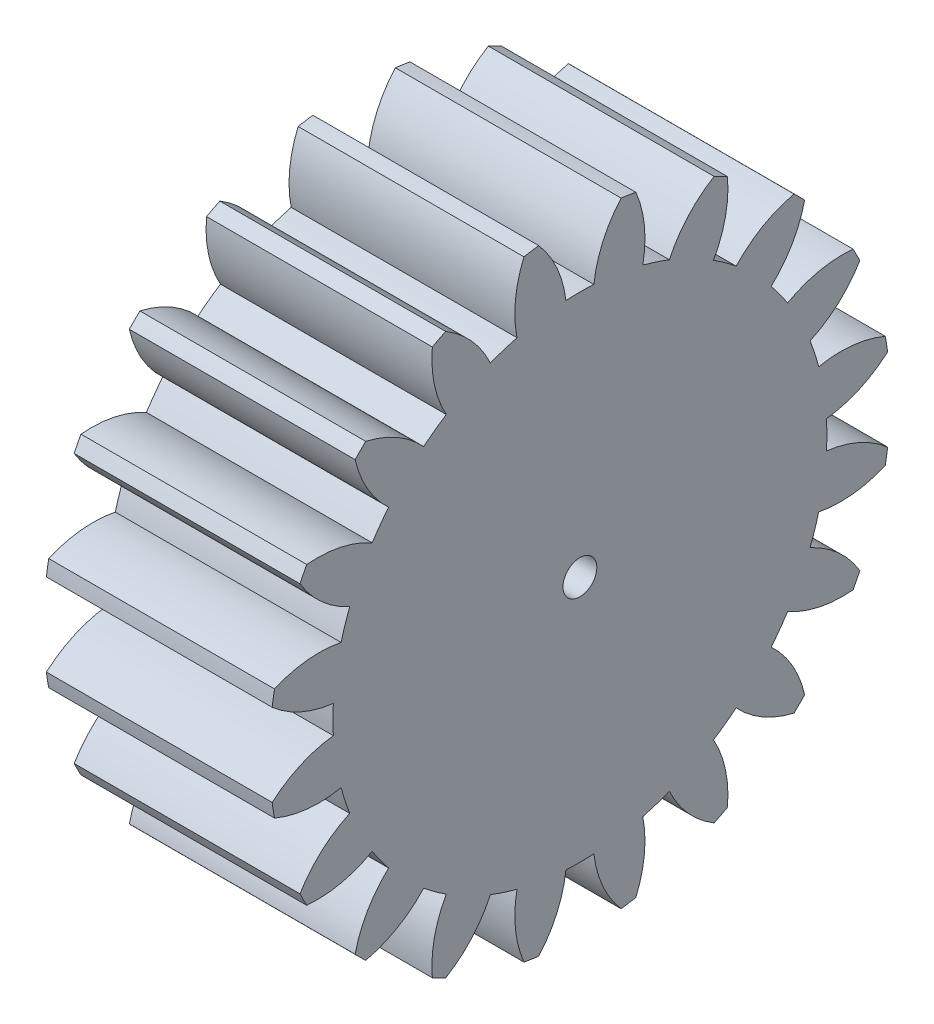
SolidWorks part; units mm, degrees
ref_plane "Plane1" through (0, 0, 0) normal (0, 0, 1) x (1, 0, 0)
ref_plane "Plane2" through (0, 0, 0) normal (0, 1, 0) x (1, 0, 0)
ref_plane "Plane3" through (0, 0, 0) normal (1, 0, 0) x (0, 0, -1)
sketch "HoldingSke" plane through (0, 0, 0) normal (0, 1, 0) x (1, 0, 0)
  line L0 (0, 0) -> (0.3759, -0.1368)
  line L1 (-15, 0) -> (100, 0) construction
  line L2 (0, 0) -> (-2.1039, 2.3779)
  line L3 (0, 0) -> (-11.863, 4.5341)
  line L4 (0, 0) -> (8.1152, 2.9537)
  line L5 (0, 0) -> (-46.8476, -17.4728)
  line L6 (0, 0) -> (-16.5793, -11.1861)
  line L7 (-2.1039, 2.3779) -> (8.6586, 51.2059)
  line L8 (-76.2, 54.61) -> (-75.7, 54.61)
  line L9 (-71.009, 38.7566) -> (-53.1078, 45.2721)
  line L10 (-76.2, 71.12) -> (104.1128, 71.12)
  line L11 (0, 0) -> (-20, 0)
  line L12 (-76.2, 101.6) -> (-76.113, 101.6)
  line L13 (24.9733, 27.94) -> (52.9518, 28.4284)
  line L14 (24.9733, 27.94) -> (24.9743, 27.94)
  line L15 (24.9733, 27.94) -> (100.4006, 29.5858)
  line L16 (-63.627, -2.5) -> (-12.827, -2.5)
  circle A0 centre (0, 0) radius 1.5
  circle A1 centre (0, 0) radius 21.874
  circle A2 centre (0, 0) radius 37.5
  circle A3 centre (0, 0) radius 1.5
  dimension "MHD" = 43.748
  dimension "Hub_dia" = 75
  dimension "Bore" = 3
  dimension "MBD" = 3
  dimension "Num_teeth" = 20
  dimension "Pitch" = 0.4
  dimension "Overall_len" = 50
  dimension "Show_teeth" = 20
  dimension "Thickness" = 20
  dimension "OAL" = 50.0001
  dimension "T_dim" = 0.5
  dimension "Ap" = 20
  dimension "H" = 19.05
  dimension "Pitch_radius" = 180.3128
  dimension "Width" = 20
  dimension "Backlash" = 0.087
  dimension "Addendum_fac" = 1
  dimension "Dedendum_fac" = 1.25
  dimension "Clearance_fac" = 0.25
  dimension "Dedendum_add" = 0.001
  dimension "Module" = 2.5
sketch "BasProSke" plane through (0, 0, 0) normal (0, 1, 0) x (1, 0, 0)
  line L0 (-10, 0) -> (60, 0) construction
  line L1 (0, 0) -> (0, 27.5)
  line L2 (0, 0) -> (20, 0)
  line L3 (20, 0) -> (20, 27.5)
  line L4 (20, 27.5) -> (0, 27.5)
  dimension "Thickness" = 20
  dimension "Diameter" = 55
revolve "Base-Revolve" add sketch "BasProSke" angle 360 about L0
sketch "TooCutSke" plane through (0, 0, 0) normal (1, 0, 0) x (0, 0, -1)
  line L1 (0, 0) -> (0, 107) construction
  line L2 (0, 0) -> (-2.1137, 24.9105) construction
  line L3 (0, 0) -> (-7.8012, 49.2549) construction
  line L4 (-2.1137, 24.9105) -> (-3.9006, 24.6275) construction
  arc A0 (1.2377, 21.839) -> (-1.2377, 21.839) centre (0, 0) ccw
  arc A1 (3.6672, 27.28) -> (-3.6672, 27.28) centre (0, 0) ccw
  circle A2 centre (0, 0) radius 25 construction
  circle A3 centre (0, 0) radius 23.4923 construction
  arc A4 (-1.2377, 21.839) -> (-3.6672, 27.28) centre (-11.1689, 20.6675) ccw
  arc A5 (3.6672, 27.28) -> (1.2377, 21.839) centre (11.1689, 20.6675) ccw
  dimension "Root_dia" = 43.748
  dimension "Overcut_dia" = 55.0508
  dimension "Pitch_dia" = 50
  dimension "Base_dia" = 46.9846
  dimension "Flank_rad" = 10
  dimension "Half_ang" = 9
  dimension "Half_CT" = 1.8092
extrude "ToothCut" cut sketch "TooCutSke" along normal through all
fillet "Breaks" [suppressed] radius 0.05
fillet "RootFillets" [suppressed] radius 0.626
pattern_circular "TeethCuts" count 20 every 18 about axis through (-10, 0, 0) along (1, 0, 0) of "ToothCut", "RootFillets", "Breaks"
sketch "HubNeaOneSke" plane through (0, 0, 0) normal (-1, 0, 0) x (0, 0, 1)
  circle A0 centre (0, 0) radius 21.874
  dimension "Diameter" = 43.748
extrude "HubNearOne" [suppressed] add sketch "HubNeaOneSke" along normal blind 30.0001
sketch "HubNeaBotSke" plane through (0, 0, 0) normal (-1, 0, 0) x (0, 0, 1)
  circle A0 centre (0, 0) radius 21.874
  dimension "Diameter" = 43.748
extrude "HubNearBoth" [suppressed] add sketch "HubNeaBotSke" along normal blind 15
ref_plane "FarPln" through (20, 0, 0) normal (1, 0, 0) x (0, 0, -1)
sketch "HubFarSke" plane through (20, 0, 0) normal (1, 0, 0) x (0, 0, -1)
  circle A0 centre (0, 0) radius 21.874
  dimension "Diameter" = 43.748
extrude "HubFar" [suppressed] add sketch "HubFarSke" along normal blind 15
sketch "BorSke" plane through (0, 0, 0) normal (1, 0, 0) x (0, 0, -1)
  circle A0 centre (0, 0) radius 1.5
  dimension "Diameter" = 3
extrude "Bore" cut sketch "BorSke" along normal mid plane 100.0001
sketch "KeySke" plane through (0, 0, 0) normal (1, 0, 0) x (0, 0, -1)
  line L0 (-0.6, 0) -> (-0.6, 2)
  line L1 (-0.6, 2) -> (0.6, 2)
  line L2 (0.6, 2) -> (0.6, 0)
  line L3 (0, 0) -> (0, 34) construction
  line L4 (-0.6, 0) -> (0.6, 0)
  dimension "Offset" = 2
  dimension "Width" = 1.2
extrude "Keyway" [suppressed] cut sketch "KeySke" along normal mid plane 100.0001
pattern_circular "Keyway2" [suppressed] count 2 every 90 about axis through (-10, 0, 0) along (1, 0, 0)
equation "' \"Module@HoldingSke\" = 6.35"
equation "' \"Num_teeth@HoldingSke\" = 12"
equation "' \"Ap@HoldingSke\" =  20"
equation "' \"Ap@HoldingSke\" = 20"
equation "' \"Width@HoldingSke\" = 0.5 * 25.4"
equation "' \"Hub_dia@HoldingSke\"= 1 * 25.4"
equation "' \"Hub_dia@HoldingSke\" = 1 * 25.4"
equation "' \"Overall_len@HoldingSke\" = 1.0 * 25.4"
equation "' \"Bore@HoldingSke\" = 0.75 * 25.4"
equation "' \"T_dim@HoldingSke\" = 0.1 * 25.4"
equation "' \"Width@KeySke\" = 0.25 * 25.4"
equation "' \"Show_teeth@HoldingSke\" = 13"
equation "' \"Backlash@HoldingSke\" = 0.009 * 25.4"
equation "' \"Addendum_fac@HoldingSke\" = 1.0"
equation "' \"Dedendum_fac@HoldingSke\" = 1.25"
equation "' \"Dedendum_add@HoldingSke\" = 0.00005 * 25.4"
equation "' \"Clearance_fac@HoldingSke\" = 0.25"
equation "\"Pitch@HoldingSke\" = 1 / \"Module@HoldingSke\""
equation "\"Overcut_dia@TooCutSke\" = (\"Num_teeth@HoldingSke\" + 2 * \"Addendum_fac@HoldingSke\") / \"Pitch@HoldingSke\" + 0.002 * 25.4"
equation "\"Pitch_dia@TooCutSke\" = \"Num_teeth@HoldingSke\" / \"Pitch@HoldingSke\""
equation "\"Base_dia@TooCutSke\" = \"Num_teeth@HoldingSke\" / \"Pitch@HoldingSke\" * cos((\"Ap@HoldingSke\"  * 3.14159265 / 180))"
equation "\"Root_dia@TooCutSke\" = (\"Num_teeth@HoldingSke\" + 2) / \"Pitch@HoldingSke\" - 2 * (\"Addendum_fac@HoldingSke\" + \"Dedendum_fac@HoldingSke\") / \"Pitch@HoldingSke\" - \"Dedendum_add@HoldingSke\" * 2"
equation "\"Half_ang@TooCutSke\" = 180 / \"Num_teeth@HoldingSke\""
equation "\"Half_CT@TooCutSke\" = \"Num_teeth@HoldingSke\" / \"Pitch@HoldingSke\" * sin((3.14159265 / 2 / \"Num_teeth@HoldingSke\")) / 2 - 7 * \"Backlash@HoldingSke\" / 4"
equation "\"Flank_rad@TooCutSke\" = \"Num_teeth@HoldingSke\" / \"Pitch@HoldingSke\" / 5"
equation "\"Radius@RootFillets\" = \"Clearance_fac@HoldingSke\" / \"Pitch@HoldingSke\" + \"Dedendum_add@HoldingSke\""
equation "\"Break_rad@Breaks\" = 0.02 / \"Pitch@HoldingSke\""
equation "\"Thickness@HoldingSke\" = \"Width@HoldingSke\""
equation "\"OAL@HoldingSke\" = \"Thickness@HoldingSke\""
equation "\"MHD@HoldingSke\" = (\"Num_teeth@HoldingSke\" + 2) / \"Pitch@HoldingSke\" - 2 * (\"Addendum_fac@HoldingSke\" + \"Dedendum_fac@HoldingSke\")  / \"Pitch@HoldingSke\" - \"Dedendum_add@HoldingSke\" * 2"
equation "\"MBD@HoldingSke\" = (\"Num_teeth@HoldingSke\" + 2) / \"Pitch@HoldingSke\" - 2 * (\"Addendum_fac@HoldingSke\" + \"Dedendum_fac@HoldingSke\")  / \"Pitch@HoldingSke\" - \"Dedendum_add@HoldingSke\" * 2 - 0.002 * 25.4"
equation "\"MHD@HoldingSke\" = ((sgn( \"MHD@HoldingSke\" - \"Hub_dia@HoldingSke\" )-1)*( \"MHD@HoldingSke\" - \"Hub_dia@HoldingSke\" ))/-2+ \"Hub_dia@HoldingSke\""
equation "\"MBD@HoldingSke\" = ((sgn( \"MBD@HoldingSke\" - \"Bore@HoldingSke\" )-1)*( \"MBD@HoldingSke\" - \"Bore@HoldingSke\" ))/-2+ \"Bore@HoldingSke\""
equation "\"OAL@HoldingSke\" = ((sgn( \"OAL@HoldingSke\" - \"Overall_len@HoldingSke\" )+1)*( \"OAL@HoldingSke\" - \"Overall_len@HoldingSke\" ))/2 + \"Overall_len@HoldingSke\" + 0.000002 * 25.4"
equation "\"Num_teeth@TeethCuts\" = int( \"Show_teeth@HoldingSke\" ) + 1"
equation "\"Num_teeth@TeethCuts\" = ((sgn( \"Num_teeth@TeethCuts\" - \"Num_teeth@HoldingSke\" )-1)*( \"Num_teeth@TeethCuts\" - \"Num_teeth@HoldingSke\" ))/-2+ \"Num_teeth@HoldingSke\""
equation "\"Num_teeth@TeethCuts\" = ((sgn( \"Num_teeth@TeethCuts\" - 2.0)+1)*( \"Num_teeth@TeethCuts\" - 2.0))/2 +2.0"
equation "\"Angle@TeethCuts\" = 360.0 / \"Num_teeth@HoldingSke\""
equation "\"Diameter@BasProSke\" = (\"Num_teeth@HoldingSke\" + 2 * \"Addendum_fac@HoldingSke\") / \"Pitch@HoldingSke\""
equation "\"Thickness@BasProSke\"  = \"Thickness@HoldingSke\""
equation "' \"Fillet_rad@BasProSke\" =  \"Thickness@HoldingSke\" * 0.05"
equation "' \"Fillet_rad@BasProSke\" = \"Thickness@HoldingSke\" * 0.05"
equation "\"MHD@HoldingSke\" = ((sgn( \"MHD@HoldingSke\" - \"Root_dia@TooCutSke\" )-1)*( \"MHD@HoldingSke\" - \"Root_dia@TooCutSke\" ))/-2+ \"Root_dia@TooCutSke\""
equation "\"Diameter@HubNeaOneSke\" = \"MHD@HoldingSke\""
equation "\"Length@HubNearOne\" = \"OAL@HoldingSke\" - \"Thickness@BasProSke\""
equation "\"Diameter@HubNeaBotSke\" = \"MHD@HoldingSke\""
equation "\"Length@HubNearBoth\" = ( \"OAL@HoldingSke\" - \"Thickness@BasProSke\" ) / 2.0"
equation "\"Thickness@FarPln\" = \"Thickness@BasProSke\""
equation "\"Diameter@HubFarSke\" = \"MHD@HoldingSke\""
equation "\"Length@HubFar\" = ( \"OAL@HoldingSke\" - \"Thickness@BasProSke\" ) / 2.0"
equation "\"Diameter@BorSke\" = \"MBD@HoldingSke\""
equation "\"D1@Bore\" = \"OAL@HoldingSke\" * 2.0"
equation "\"D1@Keyway\" = \"OAL@HoldingSke\" * 2.0"
equation "\"Offset@KeySke\" = \"T_dim@HoldingSke\" + \"MBD@HoldingSke\" / 2.0"
